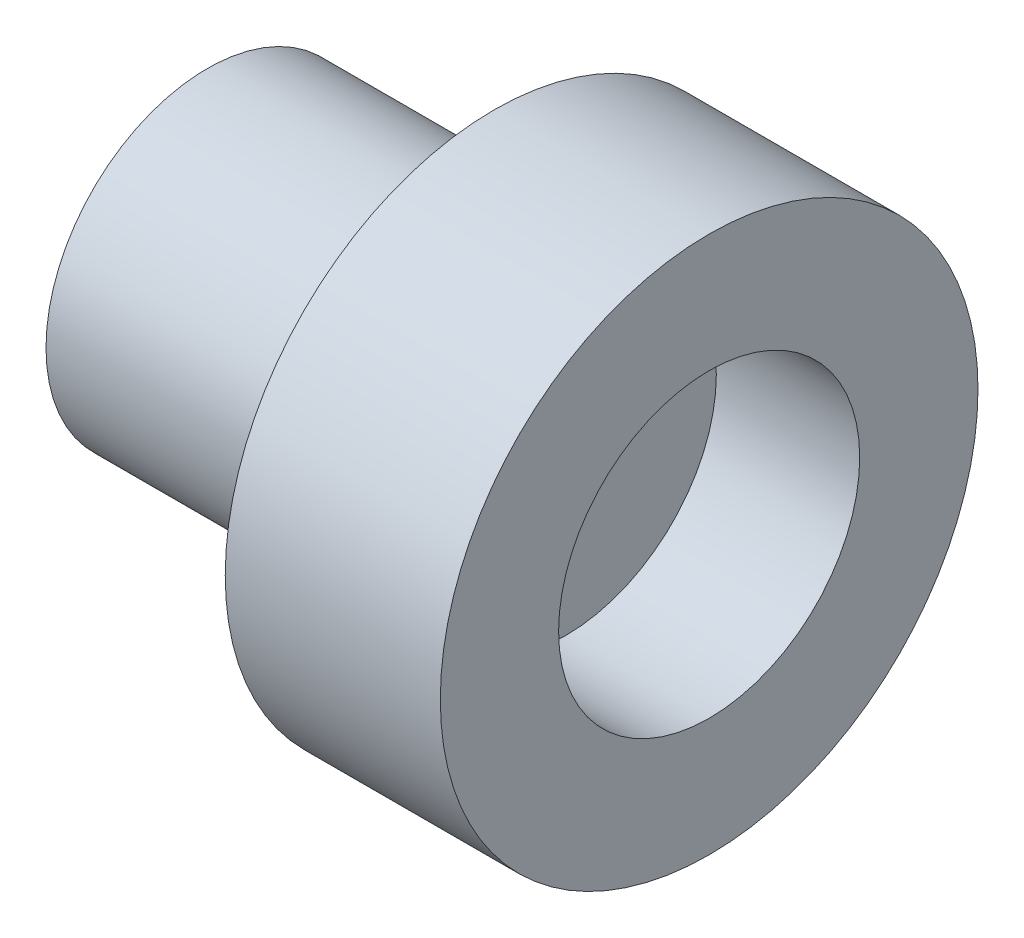
SolidWorks part; units mm, degrees
ref_plane "Front Plane" through (0, 0, 0) normal (0, 0, 1) x (1, 0, 0)
ref_plane "Top Plane" through (0, 0, 0) normal (0, 1, 0) x (1, 0, 0)
ref_plane "Right Plane" through (0, 0, 0) normal (1, 0, 0) x (0, 0, -1)
sketch "Sketch1" plane through (0, 0, 0) normal (0, 0, 1) x (1, 0, 0)
  line L0 (0, 0) -> (7.3225, 0) construction
  line L1 (0, 1.1) -> (3, 1.1)
  line L3 (5, 2.1) -> (7, 2.1)
  line L4 (7, 2.1) -> (7, 3.75)
  line L5 (7, 3.75) -> (4, 3.75)
  line L6 (4, 3.75) -> (4, 2.25)
  line L7 (4, 2.25) -> (0, 2.25)
  line L8 (0, 2.25) -> (0, 1.1)
  line L9 (5, 2.1) -> (5, 0)
  line L10 (5, 0) -> (3, 0)
  line L11 (3, 0) -> (3, 1.1)
  dimension "D1" = 4.2
  dimension "D2" = 2.2
  dimension "D3" = 4.5
  dimension "D4" = 7.5
  dimension "D5" = 3
  dimension "D6" = 2
  dimension "D7" = 4
  dimension "D8" = 3
revolve "Revolve1" add sketch "Sketch1" angle 360 about L0
fillet "Fillet1" radius 1 1 edges at (4, 0, 2.25)
